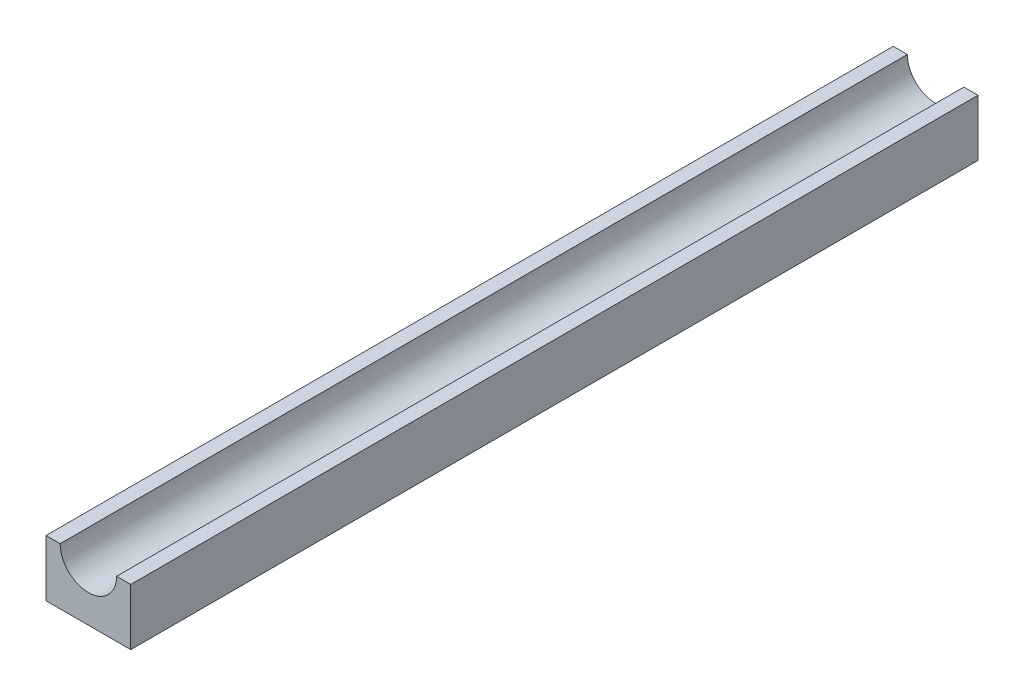
SolidWorks part; units mm, degrees
ref_plane "Front Plane" through (0, 0, 0) normal (0, 0, 1) x (1, 0, 0)
ref_plane "Top Plane" through (0, 0, 0) normal (0, 1, 0) x (1, 0, 0)
ref_plane "Right Plane" through (0, 0, 0) normal (1, 0, 0) x (0, 0, -1)
sketch "Sketch1" plane through (0, 0, 0) normal (0, 0, 1) x (1, 0, 0)
  line L1 (-7.5, 5) -> (7.5, 5)
  line L2 (-7.5, 5) -> (-7.5, -5)
  line L3 (-7.5, -5) -> (7.5, -5)
  line L4 (7.5, 5) -> (7.5, -5)
  line L5 (-7.5, 5) -> (7.5, -5) construction
  line L6 (-7.5, -5) -> (7.5, 5) construction
  circle A1 centre (0, 5) radius 5
  point P0 (0, 0)
  dimension "D3" = 10
  dimension "D1" = 10
  dimension "D2" = 15
extrude "Boss-Extrude1" add sketch "Sketch1" along normal blind 150
ref_plane "Plane1" through (0, 0, 15) normal (0, 0, -1) x (-1, 0, 0)
sketch "Sketch3" plane through (0, 0, 15) normal (0, 0, -1) x (-1, 0, 0)
  line L0 (7.5, -5) -> (-7.5, -5) construction
  line L1 (1.5, -5) -> (-1.5, -5)
  line L2 (1.5, -5) -> (1.5, -7)
  line L3 (1.5, -7) -> (-1.5, -7)
  line L4 (-1.5, -5) -> (-1.5, -7)
  line L5 (1.5, -5) -> (-1.5, -7) construction
  line L6 (1.5, -7) -> (-1.5, -5) construction
  arc A0 (-1.5, -7) -> (1.5, -7) centre (0, -7) ccw
  circle A1 centre (0, -7) radius 0.5
  point P0 (0, -6)
  point P7 (0, -5)
  point P8 (0, -5)
  dimension "D3" = 1
  dimension "D1" = 2
  dimension "D2" = 3
ref_plane "Plane2" through (0, 0, 82.5) normal (0, 0, 1) x (1, 0, 0)
ref_plane "Plane3" through (0, 0, 0) normal (-1, 0, 0) x (0, 0, 1)
sketch "Sketch6" plane through (0, 0, 0) normal (-1, 0, 0) x (0, 0, 1)
  line L0 (150, -5) -> (0, -5) construction
  line L1 (72.5, -5) -> (77.5, -5)
  line L2 (72.5, -5) -> (72.5, -8)
  line L3 (72.5, -8) -> (77.5, -8)
  line L4 (77.5, -5) -> (77.5, -8)
  line L5 (72.5, -5) -> (77.5, -8) construction
  line L6 (72.5, -8) -> (77.5, -5) construction
  line L7 (150, -5) -> (0, -5)
  line L8 (150, 5) -> (150, -5) construction
  circle A0 centre (75, -8) radius 2.5
  point P0 (75, -6.5)
  dimension "D1" = 5
  dimension "D2" = 75
  dimension "D3" = 3
extrude "Boss-Extrude6" add sketch "Sketch6" along normal mid plane 3 contours L3 A0 | L3 A0 | A0 L4 L1 L2
sketch "Sketch7" plane through (0, 0, 0) normal (-1, 0, 0) x (0, 0, 1)
  arc A0 (72.5, -8) -> (77.5, -8) centre (75, -8) ccw construction
  arc A1 (72.5, -8) -> (77.5, -8) centre (75, -8) ccw
  circle A2 centre (75, -8) radius 0.5
  dimension "D1" = 1
ref_plane "Plane4" through (0, 0, 45) normal (0, 0, -1) x (-1, 0, 0)
mirror "Mirror1" about plane through (0, 0, 45) normal (0, 0, -1) of "Boss-Extrude6"
extrude "Cut-Extrude1" cut sketch "Sketch7" against normal through all both and the other way through all contours A2
sketch "Sketch9" plane through (-1.5, 0, 0) normal (-1, 0, 0) x (0, 0, 1)
  circle A0 centre (15, -8) radius 0.5
  dimension "D1" = 1
extrude "Cut-Extrude2" cut sketch "Sketch9" against normal blind 10
